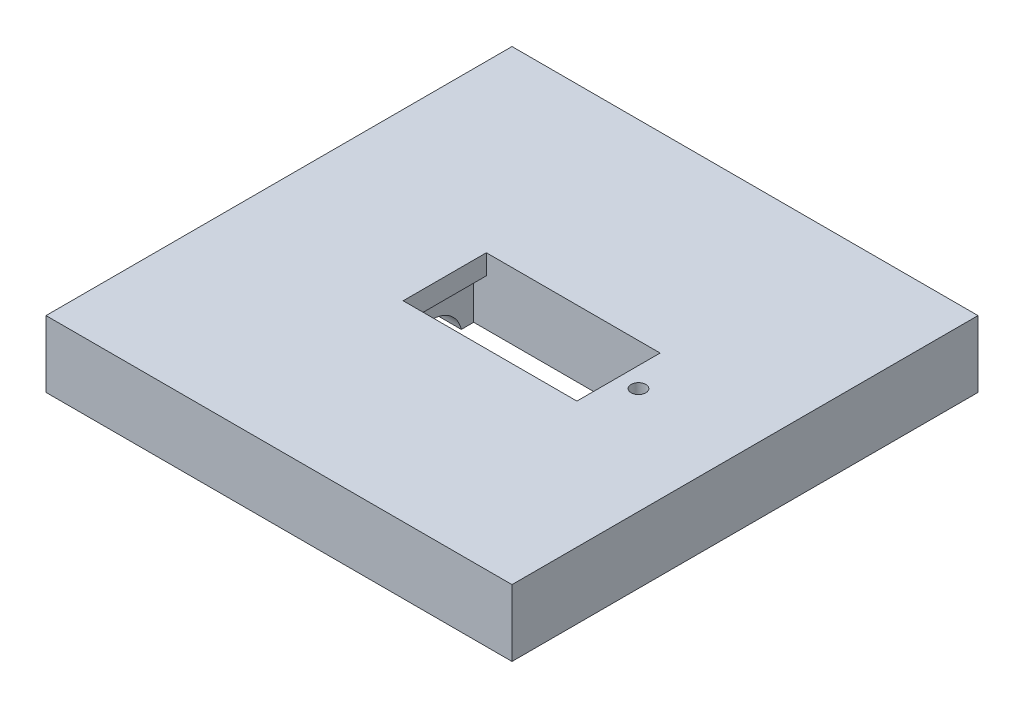
SolidWorks part; units mm, degrees
material "PLA"
ref_plane "Alzado" through (0, 0, 0) normal (0, 0, 1) x (1, 0, 0)
ref_plane "Planta" through (0, 0, 0) normal (0, 1, 0) x (1, 0, 0)
ref_plane "Vista lateral" through (0, 0, 0) normal (1, 0, 0) x (0, 0, -1)
sketch "Croquis1" plane through (0, 0, 0) normal (0, 1, 0) x (1, 0, 0)
  line L1 (-32, 32) -> (32, 32)
  line L2 (-32, 32) -> (-32, -32)
  line L3 (-32, -32) -> (32, -32)
  line L4 (32, 32) -> (32, -32)
  line L5 (-32, 32) -> (32, -32) construction
  line L6 (-32, -32) -> (32, 32) construction
  circle A0 centre (0, 0) radius 31 construction
  point P0 (0, 0)
extrude "Saliente-Extruir1" add sketch "Croquis1" along normal blind 60 contours L1 L4 L3 L2
sketch "Croquis2" plane through (0, 0, 0) normal (0, 1, 0) x (1, 0, 0)
  line L1 (-35, 35) -> (35, 35)
  line L2 (-35, 35) -> (-35, -35)
  line L3 (-35, -35) -> (35, -35)
  line L4 (35, 35) -> (35, -35)
  line L5 (-35, 35) -> (35, -35) construction
  line L6 (-35, -35) -> (35, 35) construction
  line L7 (-32, -32) -> (32, -32)
  line L8 (-32, -32) -> (-32, 32)
  line L9 (-32, 32) -> (32, 32)
  line L10 (32, -32) -> (32, 32)
  line L11 (-32, -32) -> (32, 32) construction
  line L12 (-32, 32) -> (32, -32) construction
  point P0 (0, 0)
  point P6 (0, 0)
extrude "Saliente-Extruir2" add sketch "Croquis2" along normal blind 64
sketch "Croquis3" plane through (0, 64, 0) normal (0, 1, 0) x (1, 0, 0)
  line L0 (0, 0) -> (16, 0) construction
  line L1 (0, 0) -> (0, 3.6) construction
  line L2 (0, 1.8) -> (1.9, 1.8) construction
  line L3 (1.9, 0) -> (1.9, 1.8) construction
  line L4 (1.9, 1.8) -> (1.9, 3.0578) construction
  line L5 (16, -2) -> (16, 2)
  line L6 (1.9, 3.0578) -> (16, 2)
  line L7 (1.9, -3.0578) -> (16, -2)
  line L8 (-1.9, -3.0578) -> (-16, -2)
  line L9 (-16, -2) -> (-16, 2)
  line L10 (-1.9, 3.0578) -> (-16, 2)
  circle A0 centre (0, 0) radius 3.6 construction
  arc A1 (-1.9, 3.0578) -> (1.9, 3.0578) centre (0, 0) cw
  arc A2 (-1.9, -3.0578) -> (1.9, -3.0578) centre (0, 0) ccw
sketch "Croquis4" plane through (0, 60, 0) normal (0, 1, 0) x (1, 0, 0)
  line L0 (0, 0) -> (-7, 0) construction
  line L1 (-7, 6) -> (-7, -6)
  line L3 (16, -6) -> (16, 6)
  line L5 (-7, 6) -> (-7, 6.25)
  line L6 (16, -6) -> (16, -6.25)
  line L7 (16, -6.25) -> (-7, -6.25)
  line L8 (-7, -6.25) -> (-7, -6)
  line L9 (-7, 6.25) -> (16, 6.25)
  line L10 (16, 6.25) -> (16, 6)
  point P8 (16, 0)
extrude "Cortar-Extruir1" cut sketch "Croquis4" against normal blind 21
sketch "Croquis5" plane through (0, 60, 0) normal (0, 1, 0) x (1, 0, 0)
  line L0 (16, 0) -> (19, 0) construction
  line L1 (-7, 0) -> (-9, 0) construction
  line L2 (-7, 6.25) -> (-7, -6.25) construction
  circle A0 centre (19, 0) radius 1.1
  circle A1 centre (-9, 0) radius 1.1
extrude "Cortar-Extruir2" cut sketch "Croquis5" against normal blind 10
sketch "Croquis10" plane through (-7, 0, 0) normal (1, 0, 0) x (0, 0, -1)
  line L0 (0, 39) -> (0, 44)
  line L2 (0, 39) -> (0, 60) construction
  line L3 (6.25, 39) -> (-6.25, 39) construction
  line L4 (6.25, 60) -> (-6.25, 60) construction
  circle A0 centre (0, 44) radius 4.5
extrude "Cortar-Extruir3" cut sketch "Croquis10" against normal up to next contours L2 L0 A0 | L0 L2 A0
sketch "Croquis11" plane through (0, 0, 0) normal (0, -1, 0) x (1, 0, 0)
  line L1 (-35, 35) -> (35, 35)
  line L2 (-35, 35) -> (-35, -35)
  line L3 (-35, -35) -> (35, -35)
  line L4 (35, 35) -> (35, -35)
  line L5 (-35, 35) -> (35, -35) construction
  line L6 (-35, -35) -> (35, 35) construction
  point P0 (0, 0)
extrude "Cortar-Extruir4" cut sketch "Croquis11" against normal blind 30
sketch "Croquis12" plane through (0, 30, 0) normal (0, -1, 0) x (1, 0, 0)
  line L0 (0, 0) -> (0, 22.1) construction
  line L1 (0, 22.1) -> (16, 22.1) construction
  line L2 (16, 20.2) -> (16, 24) construction
  line L3 (1.9, 0) -> (1.9, 22.1) construction
  line L4 (1.9, 22.1) -> (1.9, 25.0578) construction
  line L5 (1.9, 25.0578) -> (16, 24) construction
  line L6 (1.9, 19.1422) -> (16, 20.2) construction
  line L7 (-1.9, 25.0578) -> (-16, 24) construction
  line L8 (-16, 20.2) -> (-16, 24) construction
  line L9 (-1.9, 19.1422) -> (-16, 20.2) construction
  line L10 (0, 22.1) -> (-7, 22.1) construction
  line L11 (-7, 28.2) -> (-7, 16)
  line L12 (-7, 16) -> (16, 16)
  line L13 (16, 16) -> (16, 28.2)
  line L14 (-7, 28.2) -> (16, 28.2)
  line L15 (0, 0) -> (19.54, 0) construction
  circle A0 centre (0, 22.1) radius 3.5155 construction
  arc A1 (1.9, 25.0578) -> (-1.9, 25.0578) centre (0, 22.1) ccw construction
  arc A2 (1.9, 19.1422) -> (-1.9, 19.1422) centre (0, 22.1) cw construction
  circle A3 centre (0, 22.1) radius 24 construction
  circle A4 centre (0, -22.1) radius 24 construction
extrude "Cortar-Extruir5" cut sketch "Croquis12" against normal blind 21
sketch "Croquis13" plane through (-7, 0, 0) normal (1, 0, 0) x (0, 0, -1)
  line L0 (-22.1, 30) -> (-22.1, 46) construction
  line L2 (-28.2, 30) -> (-16, 30) construction
  circle A0 centre (-22.1, 46) radius 4.5
extrude "Cortar-Extruir6" cut sketch "Croquis13" against normal up to next
sketch "Croquis14" plane through (0, 30, 0) normal (0, -1, 0) x (1, 0, 0)
  line L0 (16, 22.1) -> (19, 22.1) construction
  line L1 (-7, 22.1) -> (-9, 22.1) construction
  circle A0 centre (19, 22.1) radius 1.1
  circle A1 centre (-9, 22.1) radius 1.1
extrude "Cortar-Extruir7" cut sketch "Croquis14" against normal blind 10
sketch "Croquis15" plane through (0, 30, 0) normal (0, -1, 0) x (1, 0, 0)
  circle A0 centre (0, -22.1) radius 3.7
extrude "Cortar-Extruir8" cut sketch "Croquis15" against normal blind 10 contours A0
sketch "Croquis16" plane through (0, 60, 0) normal (0, 1, 0) x (1, 0, 0)
  line L1 (-32, -32) -> (32, -32)
  line L2 (-32, -32) -> (-32, 32)
  line L3 (-32, 32) -> (32, 32)
  line L4 (32, -32) -> (32, 32)
  line L5 (-32, -32) -> (32, 32) construction
  line L6 (-32, 32) -> (32, -32) construction
  point P0 (0, 0)
extrude "Cortar-Extruir9" cut sketch "Croquis16" against normal blind 5
sketch "Croquis17" plane through (-7, 0, 0) normal (1, 0, 0) x (0, 0, -1)
  line L0 (6.25, 55) -> (6.25, 51.9987) construction
  line L1 (6.25, 39) -> (6.25, 55) construction
  line L2 (6.25, 51.9987) -> (-6.25, 51.9987)
  line L3 (-6.25, 39) -> (-6.25, 55) construction
  line L4 (-6.25, 51.9987) -> (-6.25, 39)
  line L5 (-6.25, 39) -> (6.25, 39)
  line L6 (6.25, 39) -> (-6.25, 39) construction
  line L7 (6.25, 39) -> (6.25, 51.9987)
extrude "Cortar-Extruir10" cut sketch "Croquis17" against normal blind 5
sketch "Croquis18" plane through (35, 0, 0) normal (1, 0, 0) x (0, 0, -1)
  line L0 (35, 64) -> (35, 30) construction
  line L1 (-35, 64) -> (35, 64)
  line L2 (-35, 64) -> (-35, 55)
  line L3 (-35, 55) -> (35, 55)
  line L4 (35, 64) -> (35, 55)
  line L5 (-35, 30) -> (-35, 35.0002)
  line L6 (-35, 64) -> (-35, 30) construction
  line L7 (-35, 35.0002) -> (35, 35.0002)
  line L8 (35, 35.0002) -> (35, 30)
  line L9 (-1.9, 30) -> (46.1, 30) construction
  line L10 (35, 30) -> (-35, 30)
extrude "Cortar-Extruir11" cut sketch "Croquis18" against normal up to next
sketch "Croquis19" plane through (-7, 0, 0) normal (1, 0, 0) x (0, 0, -1)
  line L0 (-16, 30) -> (-16, 33) construction
  line L1 (-16, 51) -> (-16, 35.0002) construction
  line L2 (-16, 51) -> (-28.2, 51)
  line L7 (-22.1, 35.0002) -> (-22.1, 38.0002) construction
  line L8 (-16, 35.0002) -> (-28.2, 35.0002) construction
  line L9 (-22.1, 38.0002) -> (-16, 38.0002)
  line L10 (-22.1, 38.0002) -> (-28.2, 38.0002)
  line L11 (-28.2, 51) -> (-28.2, 38.0002)
  line L12 (-16, 51) -> (-16, 38.0002)
  line L13 (-22.1, 35.0002) -> (-16, 35.0002) construction
  line L14 (-16, 35.0002) -> (-16, 33) construction
extrude "Cortar-Extruir13" cut sketch "Croquis19" against normal blind 5
ref_plane "Plano1" through (0, 45.0002, 0) normal (0, -1, 0) x (-1, 0, 0)
sketch "Croquis21" plane through (0, 45.0002, 0) normal (0, -1, 0) x (-1, 0, 0)
  line L1 (-40.6571, 39.9693) -> (40.8099, 39.9693)
  line L2 (-40.6571, 39.9693) -> (-40.6571, -41.4977)
  line L3 (-40.6571, -41.4977) -> (40.8099, -41.4977)
  line L4 (40.8099, 39.9693) -> (40.8099, -41.4977)
extrude "Cortar-Extruir14" cut sketch "Croquis21" along normal up to next
sketch "Croquis22" plane through (0, 38.0002, 0) normal (0, 1, 0) x (1, 0, 0)
  line L1 (-7, -16) -> (-10.1, -16)
  line L2 (-7, -16) -> (-7, -28.2)
  line L3 (-7, -28.2) -> (-10.1, -28.2)
  line L4 (-10.1, -16) -> (-10.1, -28.2)
sketch "Croquis23" plane through (0, 51.9987, 0) normal (0, -1, 0) x (1, 0, 0)
  line L0 (-12, -6.25) -> (-7, -6.25) construction
  line L1 (-7, 6.25) -> (-10.1, 6.25)
  line L2 (-7, 6.25) -> (-7, -6.25)
  line L3 (-7, -6.25) -> (-10.1, -6.25)
  line L4 (-10.1, 6.25) -> (-10.1, -6.25)
extrude "Cortar-Extruir16" cut sketch "Croquis23" against normal up to next
